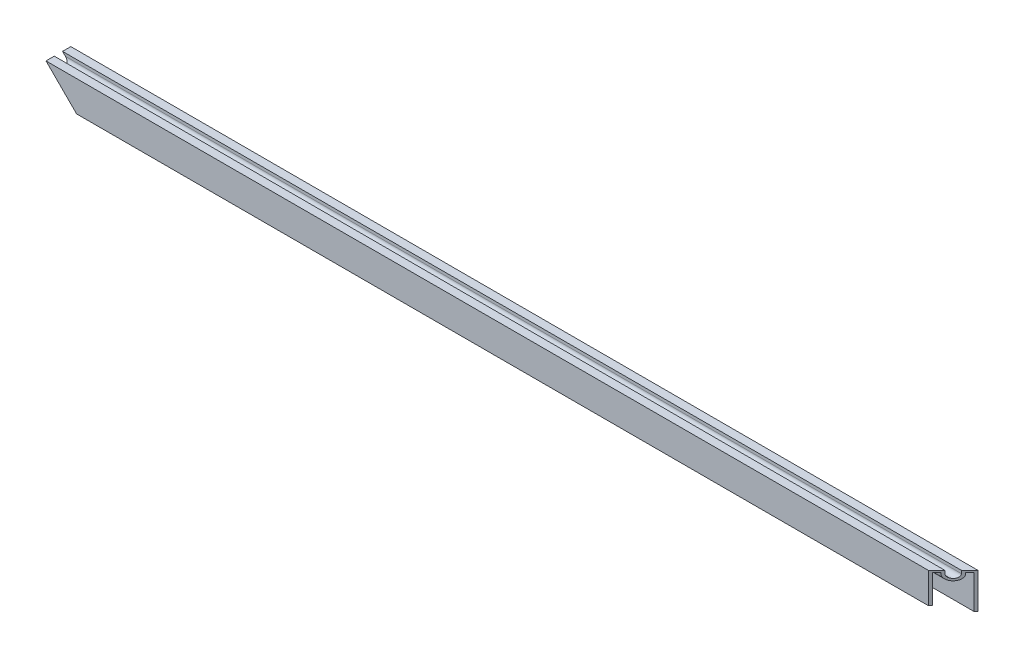
SolidWorks part; units mm, degrees
material "6063-O"
ref_plane "Front Plane" through (0, 0, 0) normal (0, 0, 1) x (1, 0, 0)
ref_plane "Top Plane" through (0, 0, 0) normal (0, 1, 0) x (1, 0, 0)
ref_plane "Right Plane" through (0, 0, 0) normal (1, 0, 0) x (0, 0, -1)
sketch "Sketch1" plane through (0, 0, 0) normal (1, 0, 0) x (0, 0, -1)
  line L0 (0, 0) -> (0, 21.844)
  line L1 (0, 21.844) -> (-5.08, 21.844)
  line L2 (-5.08, 21.844) -> (-5.08, 20.066)
  line L3 (-10.16, 20.066) -> (-10.16, 21.844)
  line L4 (-10.16, 21.844) -> (-15.24, 21.844)
  line L5 (-15.24, 21.844) -> (-15.24, 3.048)
  line L6 (-1.27, 0) -> (-1.27, 20.574)
  line L7 (-1.27, 20.574) -> (-3.81, 20.574)
  line L8 (-3.81, 20.574) -> (-3.81, 20.066)
  line L9 (-11.43, 20.066) -> (-11.43, 20.574)
  line L10 (-11.43, 20.574) -> (-13.97, 20.574)
  line L11 (-13.97, 20.574) -> (-13.97, 3.048)
  line L12 (0, 0) -> (-1.27, 0)
  line L13 (-15.24, 3.048) -> (-13.97, 3.048)
  arc A0 (-5.08, 20.066) -> (-10.16, 20.066) centre (-7.62, 20.066) cw
  arc A1 (-3.81, 20.066) -> (-11.43, 20.066) centre (-7.62, 20.066) cw
  dimension "D1" = 4.318
  dimension "D2" = 21.844
  dimension "D3" = 18.796
  dimension "D4" = 15.24
  dimension "D5" = 5.08
  dimension "D6" = 12.7
extrude "Boss-Extrude1" add sketch "Sketch1" along normal mid plane 557.2125
sketch "Sketch3" plane through (0, 21.844, 0) normal (0, 1, 0) x (1, 0, 0)
  line L0 (278.6062, 0) -> (263.3663, 0)
  line L2 (263.3663, 0) -> (278.6062, -15.24)
  line L3 (278.6062, -15.24) -> (278.6062, 0)
  line L4 (278.6062, 0) -> (-278.6062, 0) construction
extrude "Cut-Top-Right-Back" [suppressed] cut sketch "Sketch3" against normal through all
sketch "Sketch5" plane through (0, 21.844, 0) normal (0, 1, 0) x (1, 0, 0)
  line L0 (-278.6062, 0) -> (-263.3663, 0)
  line L2 (-263.3663, 0) -> (-278.6062, -15.24)
  line L3 (-278.6062, -15.24) -> (-278.6062, 0)
  line L4 (278.6062, 0) -> (-278.6062, 0) construction
extrude "Cut-Top-Left-Back" [suppressed] cut sketch "Sketch5" against normal through all
sketch "Sketch8" plane through (0, 0, 15.24) normal (0, 0, 1) x (1, 0, 0)
  line L0 (278.6062, 0) -> (256.7623, 21.844)
  line L1 (278.6062, 21.844) -> (-278.6062, 21.844) construction
  line L2 (256.7623, 21.844) -> (278.6062, 21.844)
  line L3 (278.6062, 21.844) -> (278.6062, 0)
extrude "Cut-Front-Right-Top" [suppressed] cut sketch "Sketch8" against normal through all
sketch "Sketch6" plane through (0, 0, 15.24) normal (0, 0, 1) x (1, 0, 0)
  line L0 (-278.6062, 0) -> (-256.7623, 21.844)
  line L1 (278.6062, 21.844) -> (-278.6062, 21.844) construction
  line L2 (-256.7623, 21.844) -> (-278.6062, 21.844)
  line L3 (-278.6062, 21.844) -> (-278.6062, 0)
extrude "Cut-Front-Left-Top" [suppressed] cut sketch "Sketch6" against normal through all
sketch "Sketch4" plane through (0, 21.844, 0) normal (0, 1, 0) x (1, 0, 0)
  line L0 (-278.6062, 0) -> (-263.3663, -15.24)
  line L1 (278.6062, -15.24) -> (-278.6062, -15.24) construction
  line L2 (-263.3663, -15.24) -> (-278.6062, -15.24)
  line L3 (-278.6062, -15.24) -> (-278.6062, 0)
extrude "Cut-Top-Left-Front" [suppressed] cut sketch "Sketch4" against normal through all
sketch "Sketch9" plane through (0, 0, 15.24) normal (0, 0, 1) x (1, 0, 0)
  line L0 (278.6062, 21.844) -> (256.7623, 0)
  line L1 (278.6062, 0) -> (-278.6062, 0) construction
  line L2 (256.7623, 0) -> (278.6062, 0)
  line L3 (278.6062, 0) -> (278.6062, 21.844)
extrude "Cut-Front-Right-Bottom" [suppressed] cut sketch "Sketch9" against normal through all
sketch "Sketch7" plane through (0, 0, 15.24) normal (0, 0, 1) x (1, 0, 0)
  line L0 (-278.6062, 21.844) -> (-256.7623, 0)
  line L1 (278.6062, 0) -> (-278.6062, 0) construction
  line L2 (-256.7623, 0) -> (-278.6062, 0)
  line L3 (-278.6062, 0) -> (-278.6062, 21.844)
extrude "Cut-Front-Left-Bottom" cut sketch "Sketch7" against normal through all
sketch "Sketch2" plane through (0, 21.844, 0) normal (0, 1, 0) x (1, 0, 0)
  line L0 (278.6062, 0) -> (263.3663, -15.24)
  line L1 (278.6062, -15.24) -> (-278.6062, -15.24) construction
  line L2 (263.3663, -15.24) -> (278.6062, -15.24)
  line L3 (278.6062, -15.24) -> (278.6062, 0)
extrude "Cut-Top-Right-Front" cut sketch "Sketch2" against normal through all
